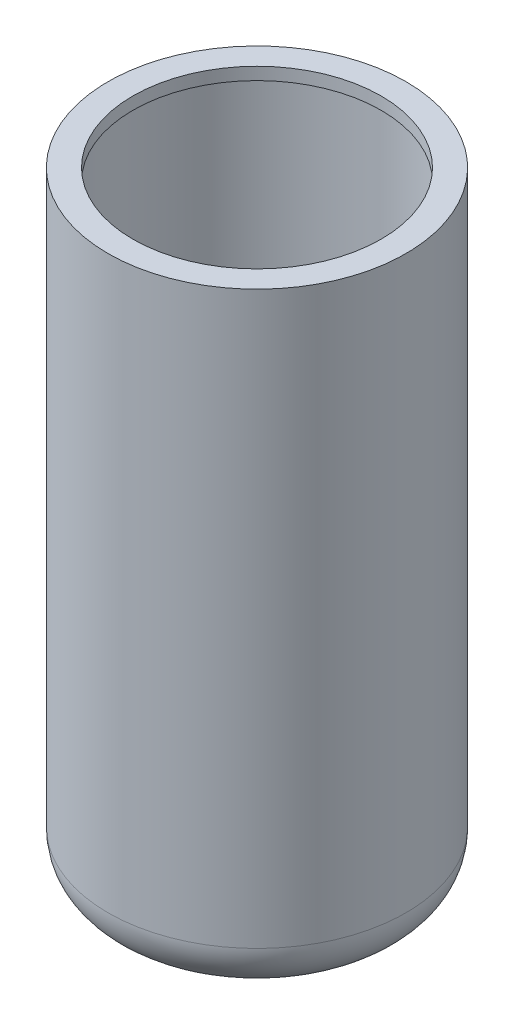
SolidWorks part; units mm, degrees
ref_plane "Front Plane" through (0, 0, 0) normal (0, 0, 1) x (1, 0, 0)
ref_plane "Top Plane" through (0, 0, 0) normal (0, 1, 0) x (1, 0, 0)
ref_plane "Right Plane" through (0, 0, 0) normal (1, 0, 0) x (0, 0, -1)
sketch "Sketch3" plane through (0, 0, 0) normal (1, 0, 0) x (0, 0, -1)
  line L1 (0, 0) -> (15.24, 0)
  line L2 (0, 0) -> (0, 63.5)
  line L3 (0, 63.5) -> (15.24, 63.5)
  line L4 (15.24, 0) -> (15.24, 63.5)
  dimension "D1" = 15.24
  dimension "D2" = 63.5
revolve "Revolve1" add sketch "Sketch3" angle 360 about L2
fillet "Fillet5" radius 5.08 1 edges at (0, 0, -15.24)
shell "Shell5" thickness 1.27
sketch "Sketch9" plane through (0, 63.5, 0) normal (0, 1, 0) x (1, 0, 0)
  circle A0 centre (0, 0) radius 12.7
  circle A1 centre (0, 0) radius 13.97
  dimension "D1" = 25.4
  dimension "D2" = 27.94
extrude "Boss-Extrude5" add sketch "Sketch9" against normal blind 1.27
